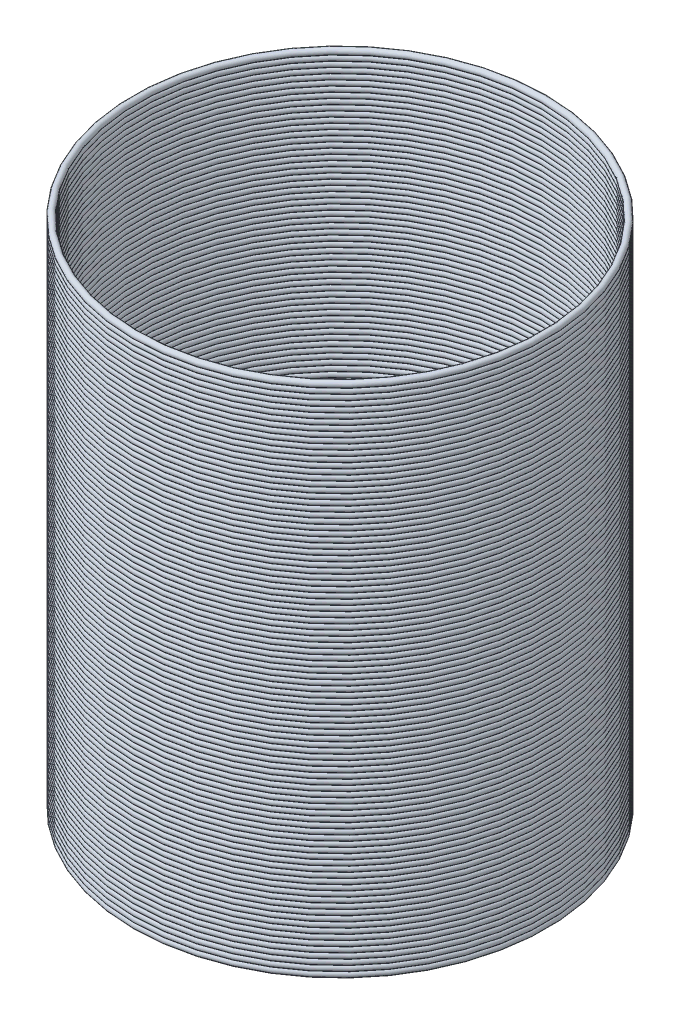
SolidWorks part; units mm, degrees
ref_plane "Front" through (0, 0, 0) normal (0, 0, 1) x (1, 0, 0)
ref_plane "Top" through (0, 0, 0) normal (0, 1, 0) x (1, 0, 0)
ref_plane "Right" through (0, 0, 0) normal (1, 0, 0) x (0, 0, -1)
sketch "Sketch1" plane through (0, 0, 0) normal (0, 1, 0) x (1, 0, 0)
  circle A0 centre (0, 0) radius 19
sketch "Sketch2" plane through (0, 0, 0) normal (0, 0, 1) x (1, 0, 0)
  line L0 (19, 0) -> (-19, 0) construction
  circle A0 centre (-19, 0) radius 0.3
sweep "Sweep1" add profiles "Sketch2" path "Sketch1"
sketch "Sketch3" plane through (0, 0, 0) normal (0, 0, 1) x (1, 0, 0)
  line L0 (0, 0) -> (0, 48.2) construction
pattern_linear "LPattern1" count 96 spacing 0.5 along (0, 1, 0) of "Sweep1"
